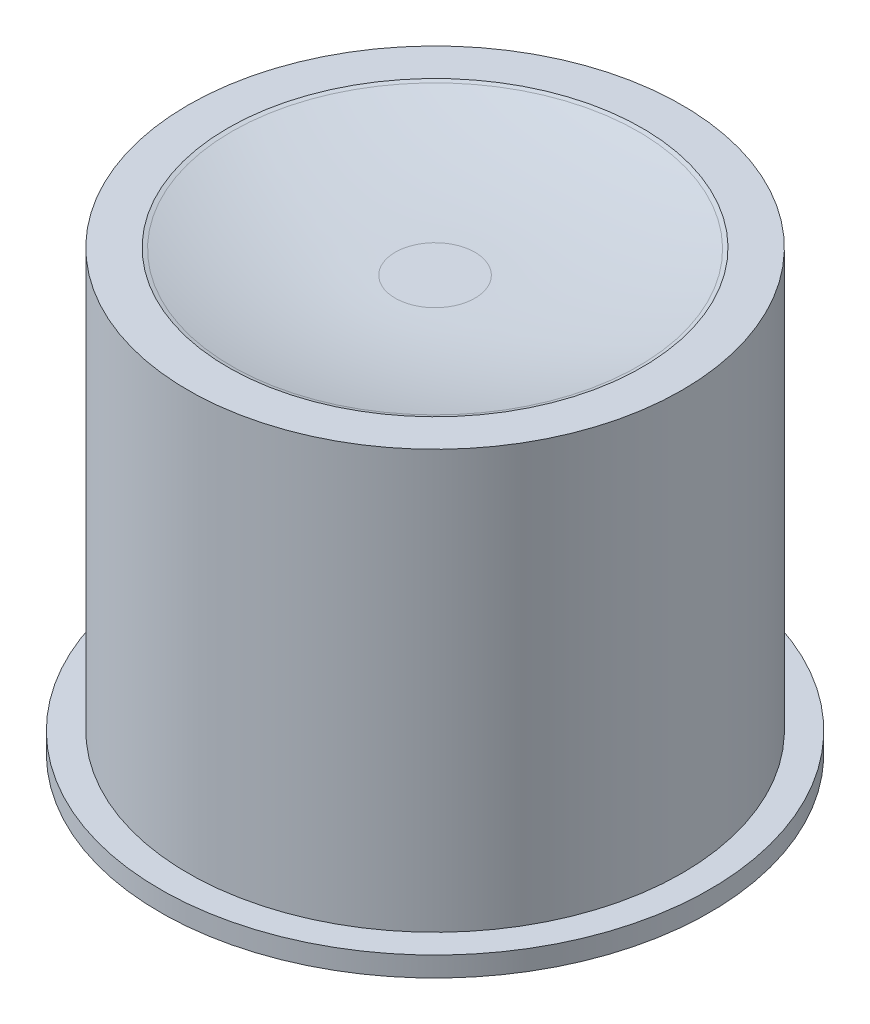
SolidWorks part; units mm, degrees
ref_plane "Front Plane" through (0, 0, 0) normal (0, 0, 1) x (1, 0, 0)
ref_plane "Top Plane" through (0, 0, 0) normal (0, 1, 0) x (1, 0, 0)
ref_plane "Right Plane" through (0, 0, 0) normal (1, 0, 0) x (0, 0, -1)
sketch "//////" plane through (0, 0, 0) normal (0, 0, 1) x (1, 0, 0)
  line L0 (0, 11.4003) -> (0, 1) construction
  line L2 (-5.2, 12) -> (-6.2, 12)
  line L3 (-6.2, 12) -> (-6.2, 1) construction
  line L4 (-6.2, 1) -> (-1.5, 1)
  line L5 (-1.5, 1) -> (-1.5, 0)
  line L6 (-1.5, 0) -> (0, 0)
  line L7 (0, 0) -> (0, 11.4003)
  line L8 (0, 11.4003) -> (-1, 11.4003)
  line L9 (-5.2, 12) -> (-5.1038, 11.9726)
  line L10 (-6.2, 1) -> (-6.9, 1)
  line L11 (-6.9, 1) -> (-6.9, 1.5)
  line L12 (-6.9, 1.5) -> (-6.2, 1.5)
  line L13 (-6.2, 1.5) -> (-6.2, 12)
  arc A0 (-1, 11.4003) -> (-5.1038, 11.9726) centre (-1, 26.4003) cw
  dimension "D1" = 15
  dimension "D3" = 1
  dimension "D2" = 6.2
  dimension "D4" = 1
  dimension "D5" = 0.1
  dimension "D6" = 11
  dimension "D7" = 1.5
  dimension "D8" = 1
  dimension "D9" = 0.5
  dimension "D10" = 0.7
revolve "Revolve1" add sketch "//////" angle 360 about L0
